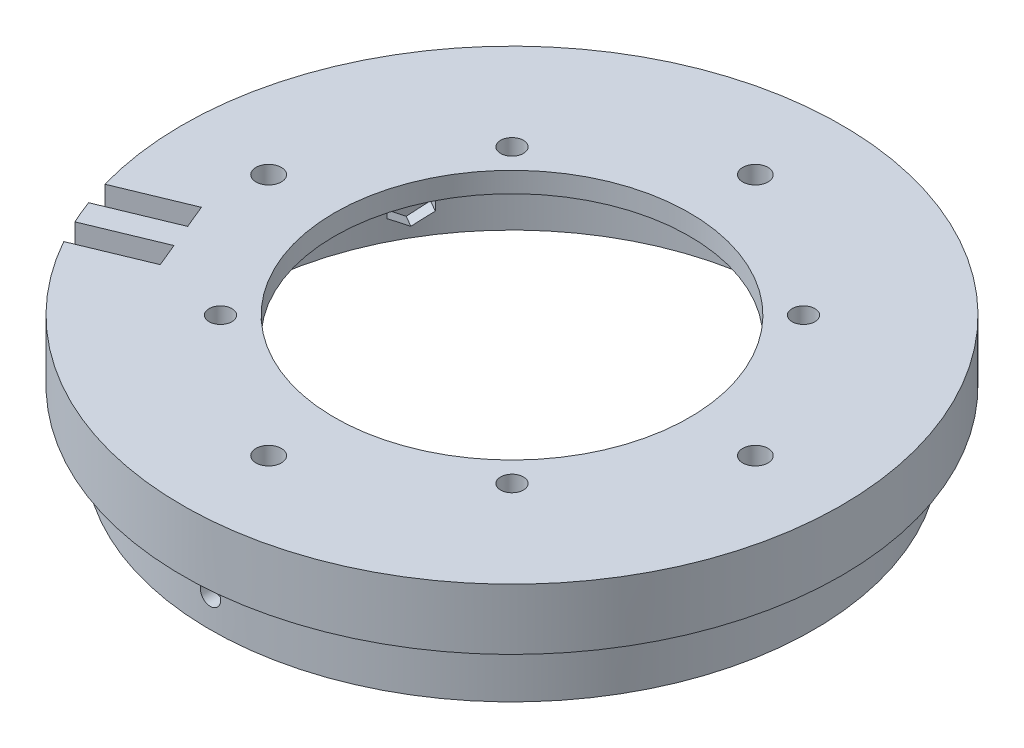
SolidWorks part; units mm, degrees
ref_plane "Front Plane" through (0, 0, 0) normal (0, 0, 1) x (1, 0, 0)
ref_plane "Top Plane" through (0, 0, 0) normal (0, 1, 0) x (1, 0, 0)
ref_plane "Right Plane" through (0, 0, 0) normal (1, 0, 0) x (0, 0, -1)
sketch "Sketch1" plane through (0, 0, 0) normal (0, 0, 1) x (1, 0, 0)
  line L0 (0, 0) -> (0, -29.4633) construction
  line L1 (-35, 0) -> (-35, -4)
  line L2 (-35, -4) -> (-54.5, -4)
  line L3 (-54.5, -4) -> (-54.5, -24)
  line L4 (-54.5, -24) -> (-59.5, -24)
  line L5 (-59.5, -24) -> (-59.5, -4)
  line L6 (-59.5, -4) -> (-65, -4)
  line L7 (-65, -4) -> (-65, 0)
  line L8 (-65, 0) -> (-35, 0)
  dimension "D1" = 4
  dimension "D2" = 130
  dimension "D3" = 70
  dimension "D4" = 5
  dimension "D5" = 119
  dimension "D6" = 20
revolve "Revolve1" add sketch "Sketch1" angle 360 about L0
sketch "Sketch2" plane through (0, -4, 0) normal (0, -1, 0) x (1, 0, 0)
  line L0 (-35, 35) -> (35, -35) construction
  line L1 (-35, 35) -> (35, 35) construction
  line L2 (-35, 35) -> (-35, -35) construction
  line L3 (-35, -35) -> (35, -35) construction
  line L4 (35, 35) -> (35, -35) construction
  line L5 (-28.75, 28.75) -> (28.75, 28.75) construction
  line L6 (28.75, 28.75) -> (28.75, -28.75) construction
  line L7 (28.75, -28.75) -> (-28.75, -28.75) construction
  line L8 (-28.75, -28.75) -> (-28.75, 28.75) construction
  line L9 (28.75, 28.75) -> (-28.75, -28.75) construction
  line L10 (-48, 0) -> (0, 0) construction
  line L11 (0, 48) -> (0, 0) construction
  line L12 (48, 0) -> (0, 0) construction
  line L13 (0, -48) -> (0, 0) construction
  circle A0 centre (-28.75, 28.75) radius 2.25
  circle A1 centre (28.75, 28.75) radius 2.25
  circle A2 centre (28.75, -28.75) radius 2.25
  circle A3 centre (-28.75, -28.75) radius 2.25
  circle A4 centre (-48, 0) radius 2.5
  circle A5 centre (0, 48) radius 2.5
  circle A6 centre (48, 0) radius 2.5
  circle A7 centre (0, -48) radius 2.5
  point P25 (0, 0)
  dimension "D3" = 4.5
  dimension "D4" = 5
  dimension "D1" = 70
  dimension "D2" = 57.5
  dimension "D5" = 48
  dimension "D6" = 4
extrude "Cut-Extrude1" cut sketch "Sketch2" against normal through all
sketch "Sketch3" plane through (0, 0, 0) normal (0, 0, 1) x (1, 0, 0)
  line L0 (-59.5, -4) -> (59.5, -4) construction
  line L1 (0, 0) -> (0, -18) construction
  line L2 (65, 0) -> (-65, 0) construction
  circle A0 centre (0, -18) radius 2
  dimension "D2" = 4
  dimension "D1" = 14
extrude "Cut-Extrude2" cut sketch "Sketch3" along normal through all
sketch "Sketch4" plane through (0, 0, 0) normal (0, 0, 1) x (1, 0, 0)
  line L1 (0, -13.9585) -> (-3.5, -15.9793)
  line L2 (-3.5, -15.9793) -> (-3.5, -20.0207)
  line L3 (-3.5, -20.0207) -> (0, -22.0415)
  line L4 (0, -22.0415) -> (3.5, -20.0207)
  line L5 (3.5, -20.0207) -> (3.5, -15.9793)
  line L6 (3.5, -15.9793) -> (0, -13.9585)
  circle A0 centre (0, -18) radius 3.5 construction
  dimension "D1" = 7
extrude "Cut-Extrude3" cut sketch "Sketch4" along normal blind 57
pattern_circular "CirPattern1" count 3 over 360 about axis through (0, 0, 0) along (0, 1, 0) of "Cut-Extrude2", "Cut-Extrude3"
sketch "Sketch5" plane through (0, -4, 0) normal (0, -1, 0) x (1, 0, 0)
  circle A0 centre (0, 0) radius 54.5
  circle A1 centre (0, 0) radius 65
  circle A2 centre (0, 0) radius 65 construction
  circle A3 centre (0, 0) radius 54.5 construction
extrude "Boss-Extrude1" add sketch "Sketch5" along normal blind 8
ref_plane "Plane1" through (-60.0522, 0, 24.8744) normal (-0.9239, 0, 0.3827) x (0.3827, 0, 0.9239)
sketch "Sketch6" plane through (-65, 0, 12.9293) normal (0.9239, 0, -0.3827) x (-0.3827, 0, -0.9239)
  line L0 (52.0707, 0) -> (-77.9293, 0) construction
  line L1 (-20.4293, 0) -> (-15.4293, 0)
  line L2 (-20.4293, 0) -> (-20.4293, -4)
  line L3 (-20.4293, -4) -> (-15.4293, -4) construction
  line L4 (-15.4293, 0) -> (-15.4293, -4)
  line L5 (-28.7981, 0) -> (-33.7981, 0) construction
  line L6 (-10.4293, 0) -> (-5.4293, 0)
  line L7 (-10.4293, 0) -> (-10.4293, -4)
  line L8 (-10.4293, -4) -> (-5.4293, -4) construction
  line L9 (-5.4293, 0) -> (-5.4293, -4)
  line L10 (-20.4293, -4) -> (-17.9293, -6.5)
  line L11 (-17.9293, -6.5) -> (-15.4293, -4)
  line L12 (-10.4293, -4) -> (-7.9293, -6.5)
  line L13 (-7.9293, -6.5) -> (-5.4293, -4)
  line L14 (-15.4293, 0) -> (-12.9293, 0) construction
  line L15 (-12.9293, 0) -> (-10.4293, 0) construction
  dimension "D1" = 5
  dimension "D2" = 4
  dimension "D3" = 5
extrude "Cut-Extrude4" cut sketch "Sketch6" along normal blind 15
